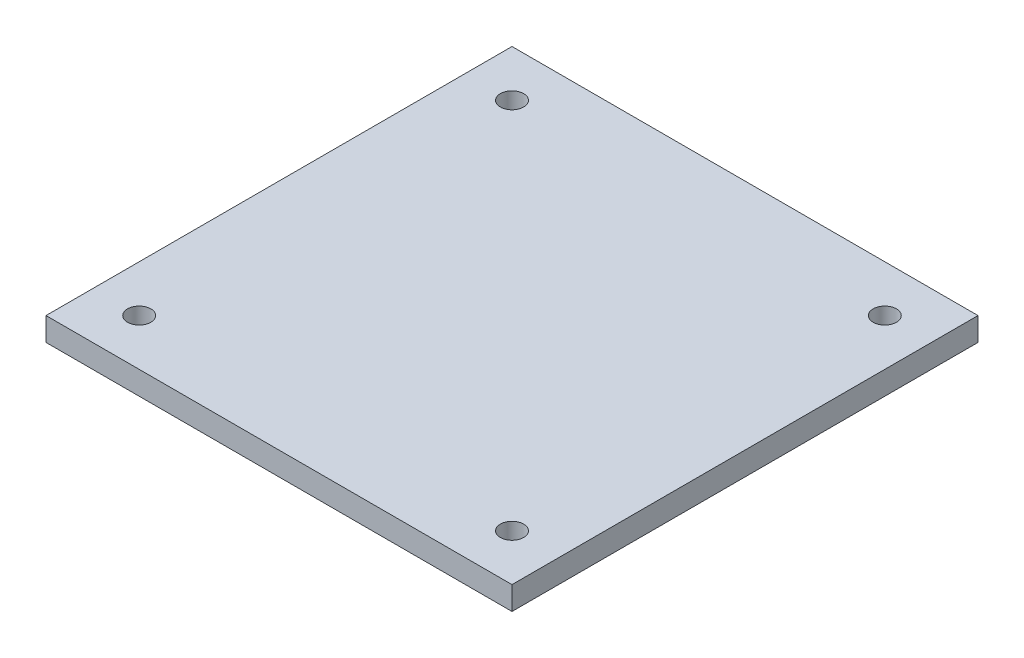
SolidWorks part; units mm, degrees
material "Plain Carbon Steel"
ref_plane "Front Plane" through (0, 0, 0) normal (0, 0, 1) x (1, 0, 0)
ref_plane "Top Plane" through (0, 0, 0) normal (0, 1, 0) x (1, 0, 0)
ref_plane "Right Plane" through (0, 0, 0) normal (1, 0, 0) x (0, 0, -1)
sketch "Sketch1" plane through (0, 0, 0) normal (0, 1, 0) x (1, 0, 0)
  line L1 (-100, -100) -> (100, -100)
  line L2 (-100, -100) -> (-100, 100)
  line L3 (-100, 100) -> (100, 100)
  line L4 (100, -100) -> (100, 100)
  line L5 (-100, -100) -> (100, 100) construction
  line L6 (-100, 100) -> (100, -100) construction
  point P0 (0, 0)
  dimension "D1" = 200
  dimension "D2" = 200
extrude "Boss-Extrude1" add sketch "Sketch1" along normal blind 10
sketch "Sketch2" plane through (0, 10, 0) normal (0, 1, 0) x (1, 0, 0)
  line L0 (-100, 100) -> (-100, -100) construction
  line L3 (100, 100) -> (-100, 100) construction
  circle A0 centre (-80, 80) radius 5
  circle A1 centre (80, 80) radius 5
  circle A2 centre (80, -80) radius 5
  circle A3 centre (-80, -80) radius 5
  dimension "D1" = 20
  dimension "D3" = 10
  dimension "D2" = 20
extrude "Cut-Extrude1" cut sketch "Sketch2" against normal blind 10
